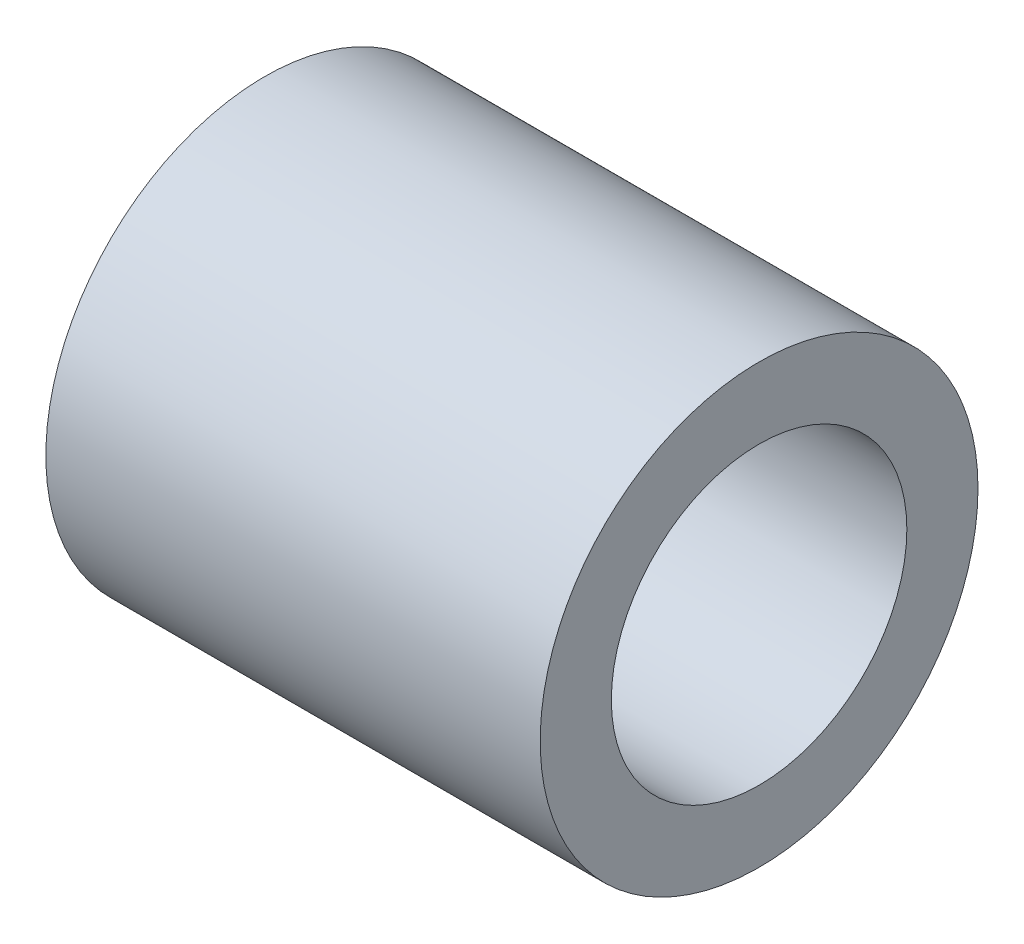
SolidWorks part; units mm, degrees
ref_plane "Front Plane" through (0, 0, 0) normal (0, 0, 1) x (1, 0, 0)
ref_plane "Top Plane" through (0, 0, 0) normal (0, 1, 0) x (1, 0, 0)
ref_plane "Right Plane" through (0, 0, 0) normal (1, 0, 0) x (0, 0, -1)
sketch "Sketch1" plane through (0, 0, 0) normal (0, 1, 0) x (1, 0, 0)
  line L0 (-19.05, 0) -> (19.05, 0)
  line L1 (15.05, 21.5) -> (15.05, -21.5)
  line L2 (-15.05, -21.5) -> (-27.05, -21.5)
  line L3 (-15.05, -21.5) -> (-15.05, 21.5)
  line L4 (-15.05, 21.5) -> (-27.05, 21.5)
  line L5 (-27.05, -21.5) -> (-27.05, 21.5)
  line L10 (4.5, -11.3898) -> (-4.5, -11.3898)
  line L11 (4.5, -11.3898) -> (4.5, 11.3898)
  line L12 (4.5, 11.3898) -> (-4.5, 11.3898)
  line L13 (-4.5, -11.3898) -> (-4.5, 11.3898)
  line L14 (4.5, -11.3898) -> (-4.5, 11.3898) construction
  line L15 (4.5, 11.3898) -> (-4.5, -11.3898) construction
  line L16 (11.05, -21.5) -> (23.05, -21.5)
  line L17 (11.05, -21.5) -> (11.05, 21.5)
  line L18 (11.05, 21.5) -> (23.05, 21.5)
  line L19 (23.05, -21.5) -> (23.05, 21.5)
  line L20 (-4.5, 6.8729) -> (-12.5, 6.8729)
  line L21 (-4.5, 6.8729) -> (-4.5, -7.6789)
  line L22 (-4.5, -7.6789) -> (-12.5, -7.6789)
  line L23 (-12.5, 6.8729) -> (-12.5, -7.6789)
  line L24 (-4.5, 6.0894) -> (-3.5, 6.0894)
  line L25 (-4.5, 6.0894) -> (-4.5, -7.0073)
  line L26 (-4.5, -7.0073) -> (-3.5, -7.0073)
  line L27 (-3.5, 6.0894) -> (-3.5, -7.0073)
  line L28 (-23.05, 21.5) -> (-23.05, -21.5)
  line L30 (-38.1, -15.5703) -> (-48.6914, -15.5703)
  line L31 (-38.1, -15.5703) -> (-38.1, 15.5703)
  line L32 (-38.1, 15.5703) -> (-48.6914, 15.5703)
  line L33 (-48.6914, -15.5703) -> (-48.6914, 15.5703)
  line L34 (-38.1, -15.5703) -> (-48.6914, 15.5703) construction
  line L35 (-38.1, 15.5703) -> (-48.6914, -15.5703) construction
  line L36 (-38.1, 15.5703) -> (-36.5125, 15.5703)
  line L37 (-38.1, 15.5703) -> (-38.1, -16.2675)
  line L38 (-38.1, -16.2675) -> (-36.5125, -16.2675)
  line L39 (-36.5125, 15.5703) -> (-36.5125, -16.2675)
  circle A0 centre (-19.05, 0) radius 2.25 construction
  circle A1 centre (19.05, 0) radius 2.25 construction
  point P9 (-15.05, 0)
  point P10 (0, 0)
  point P13 (-43.3957, 0)
  dimension "D1" = 4.5
  dimension "D2" = 38.1
  dimension "D3" = 4
  dimension "D4" = 8
  dimension "D5" = 19.05
  dimension "D6" = 9
  dimension "D7" = 8
  dimension "D8" = 4
  dimension "D9" = 8
  dimension "D10" = 1
  dimension "D11" = 4
  dimension "D12" = 43
  dimension "D13" = 4
  dimension "D14" = 1.5875
sketch "Sketch2" plane through (0, 0, 0) normal (1, 0, 0) x (0, 0, -1)
  line L0 (2.25, 0) -> (-2.25, 0) construction
  circle A0 centre (0, 0) radius 4.05
  circle A1 centre (0, 0) radius 6
  dimension "D1" = 8.1
  dimension "D2" = 12
extrude "Boss-Extrude1" add sketch "Sketch2" along normal blind 13.55
